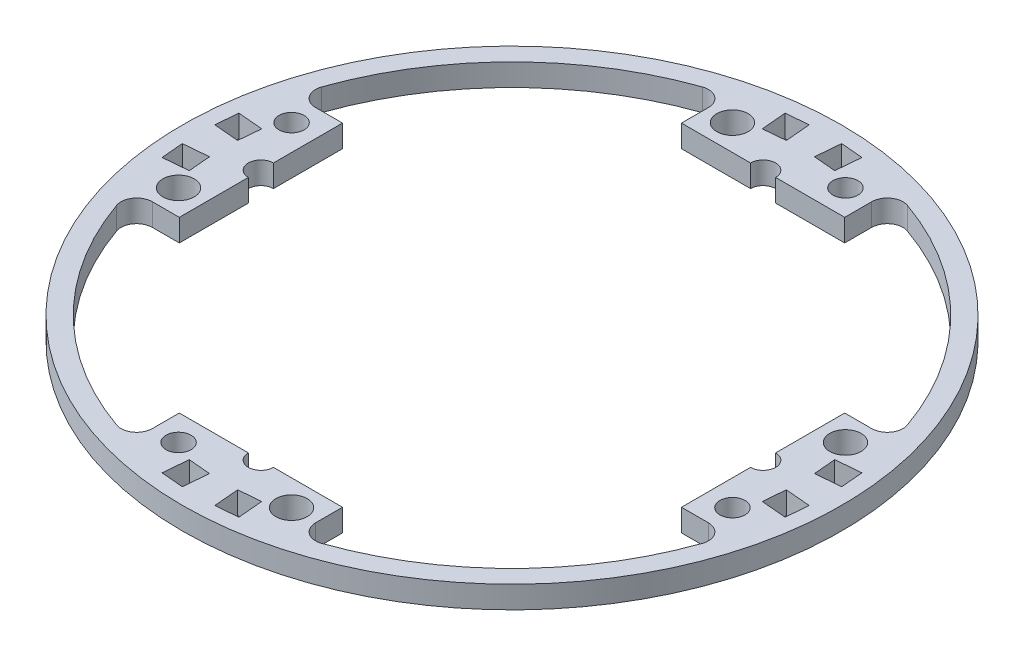
SolidWorks part; units mm, degrees
material "ABS PC"
ref_plane "Front Plane" through (0, 0, 0) normal (0, 0, 1) x (1, 0, 0)
ref_plane "Top Plane" through (0, 0, 0) normal (0, 1, 0) x (1, 0, 0)
ref_plane "Right Plane" through (0, 0, 0) normal (1, 0, 0) x (0, 0, -1)
sketch "Sketch1" plane through (0, 0, 0) normal (0, 1, 0) x (1, 0, 0)
  line L0 (-50.8, 0) -> (-50.8, 16.51)
  line L1 (-50.8, 16.51) -> (-56.2484, 16.51)
  line L2 (0, 50.8) -> (-16.51, 50.8)
  line L3 (-16.51, 50.8) -> (-16.51, 56.2484)
  line L4 (0, -55) -> (0, 55) construction
  line L6 (-55, 0) -> (55, 0) construction
  line L7 (-50.8, 0) -> (-66.675, 0)
  line L8 (0, 50.8) -> (0, 66.675)
  circle A0 centre (0, 0) radius 66.675
  arc A1 (-56.2484, 16.51) -> (-59.2452, 20.7338) centre (-56.2484, 19.685) cw
  arc A2 (-59.2452, 20.7338) -> (-20.7338, 59.2452) centre (0, 0) cw
  arc A3 (-16.51, 56.2484) -> (-20.7338, 59.2452) centre (-19.685, 56.2484) ccw
  dimension "D1" = 133.35
  dimension "D2" = 3.9065
  dimension "D5" = 3.175
  dimension "D3" = 16.51
  dimension "D4" = 15.875
extrude "Boss-Extrude1" add sketch "Sketch1" along normal blind 4.5009 contours A3 L3 L2 L8 A0 L7 L0 L1 A1 A2
sketch "Sketch2" plane through (0, 4.5009, 0) normal (0, 1, 0) x (1, 0, 0)
  line L0 (-63.4167, 3.2892) -> (-58.356, 2.8465)
  line L1 (-63.4167, 3.2892) -> (-63.0244, 7.773)
  line L2 (-58.356, 2.8465) -> (-57.9637, 7.3302)
  line L3 (-63.0244, 7.773) -> (-57.9637, 7.3302)
  line L4 (-66.4213, 5.8111) -> (0, 0) construction
  line L5 (-2.4755, 0) -> (2.4755, 0) construction
  line L6 (-63.0244, 7.773) -> (-66.1873, 8.0497) construction
  line L7 (0, 0) -> (-5.8111, 66.4213)
  line L8 (-7.3302, 57.9637) -> (-7.773, 63.0244)
  line L9 (-7.3302, 57.9637) -> (-2.8465, 58.356)
  line L10 (-7.773, 63.0244) -> (-3.2892, 63.4167)
  line L11 (-2.8465, 58.356) -> (-3.2892, 63.4167)
  line L12 (-3.2892, 63.4167) -> (-3.5659, 66.5796)
  line L13 (0, -2.4755) -> (0, 2.4755) construction
  arc A0 (0, 66.675) -> (-66.675, 0) centre (0, 0) ccw construction
  point P10 (-58.1598, 5.0883)
  point P11 (-63.2205, 5.5311)
  point P16 (-5.5311, 63.2205)
  point P19 (-5.0883, 58.1598)
  dimension "D1" = 5
  dimension "D2" = 3.175
  dimension "D3" = 5.08
  dimension "D4" = 4.5009
  dimension "D5" = 5
extrude "Cut-Extrude1" cut sketch "Sketch2" against normal blind 4.5009 contours L3 L1 L0 L2 | L10 L8 L9 L7 | L9 L11 L10 L7
pattern_circular "CirPattern1" count 4 over 360 about axis through (0, 0, 0) along (0, 1, 0) of "Boss-Extrude1", "Cut-Extrude1"
sketch "Sketch3" [suppressed] plane through (0, 4.5009, 0) normal (0, 1, 0) x (1, 0, 0)
  line L0 (0, 0) -> (-50.8, -87.9882)
  line L1 (0, 0) -> (50.8, -87.9882)
  line L2 (0, -2.4755) -> (0, 2.4755) construction
  arc A0 (-50.8, -87.9882) -> (50.8, -87.9882) centre (0, 0) ccw
  arc A1 (50.8, -87.9882) -> (-50.8, -87.9882) centre (0, 0) ccw
  dimension "D1" = 60
  dimension "D2" = 30
  dimension "D3" = 101.6
extrude "Cut-Extrude2" [suppressed] cut sketch "Sketch3" against normal through all contours L1 A1 L0
sketch "Sketch5" plane through (0, 4.5009, 0) normal (0, 1, 0) x (1, 0, 0)
  line L0 (16.51, 50.8) -> (-16.51, 50.8) construction
  line L1 (-2.54, 50.8) -> (2.54, 50.8)
  arc A0 (-2.54, 50.8) -> (2.54, 50.8) centre (0, 50.8) cw
  dimension "D1" = 2.54
extrude "Cut-Extrude3" cut sketch "Sketch5" against normal through all
pattern_circular "CirPattern2" count 4 over 360 about axis through (0, 0, 0) along (0, 1, 0) of "Cut-Extrude3"
sketch "Sketch6" plane through (0, 4.5009, 0) normal (0, 1, 0) x (1, 0, 0)
  line L0 (-2.4755, 0) -> (2.4755, 0) construction
  line L1 (0, -2.4755) -> (0, 2.4755) construction
  circle A0 centre (-56.0331, -11.43) radius 3.175
  dimension "D1" = 6.35
  dimension "D2" = 11.43
  dimension "D3" = 56.0331
extrude "Cut-Extrude4" cut sketch "Sketch6" against normal through all
pattern_circular "CirPattern3" count 4 over 360 about axis through (0, 0, 0) along (0, 1, 0) of "Cut-Extrude4"
sketch "Sketch9" plane through (0, 4.5009, 0) normal (0, 1, 0) x (1, 0, 0)
  line L0 (-11.43, 56.0331) -> (11.43, 56.0331)
  line L1 (0, -2.4755) -> (0, 2.4755) construction
  circle A0 centre (-11.43, 56.0331) radius 3.175 construction
  circle A1 centre (-11.43, 56.0331) radius 3.175
  circle A2 centre (11.43, 56.0331) radius 2.54
  point P3 (0, 56.0331)
  dimension "D1" = 5.08
extrude "Cut-Extrude5" cut sketch "Sketch9" against normal through all
pattern_circular "CirPattern4" count 4 over 360 about axis through (0, 0, 0) along (0, 1, 0) of "Cut-Extrude5"
